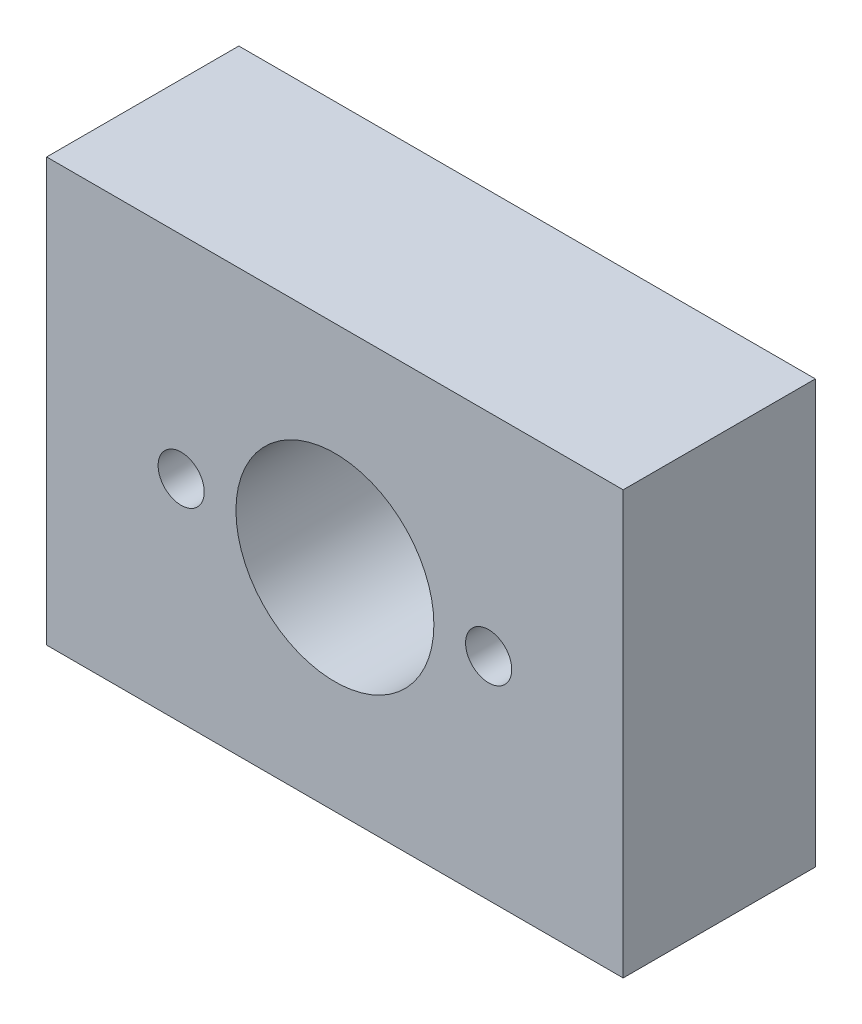
SolidWorks part; units mm, degrees
ref_plane "Front Plane" through (0, 0, 0) normal (0, 0, 1) x (1, 0, 0)
ref_plane "Top Plane" through (0, 0, 0) normal (0, 1, 0) x (1, 0, 0)
ref_plane "Right Plane" through (0, 0, 0) normal (1, 0, 0) x (0, 0, -1)
sketch "Sketch1" plane through (0, 0, 0) normal (0, 0, 1) x (1, 0, 0)
  line L1 (15, -11) -> (-15, -11)
  line L2 (15, -11) -> (15, 11)
  line L3 (15, 11) -> (-15, 11)
  line L4 (-15, -11) -> (-15, 11)
  circle A0 centre (0, 0) radius 11 construction
  circle A1 centre (0, 0) radius 5.15
  point P0 (0, 0)
  point P9 (-15, 0)
  point P10 (0, 11)
  dimension "D1" = 22
  dimension "D4" = 10.3
  dimension "D2" = 11
  dimension "D3" = 30
extrude "Boss-Extrude1" add sketch "Sketch1" along normal blind 10
sketch "Sketch2" plane through (0, -11, 0) normal (0, -1, 0) x (1, 0, 0)
  line L0 (0, 10) -> (0, 0) construction
  line L1 (-15, 10) -> (15, 10) construction
  circle A0 centre (-11, 5) radius 2
  circle A1 centre (11, 5) radius 2
  point P10 (0, 5)
  dimension "D2" = 4
  dimension "D1" = 22
extrude "Cut-Extrude1" cut sketch "Sketch2" against normal blind 10
sketch "Sketch7" plane through (0, 0, 10) normal (0, 0, 1) x (1, 0, 0)
  line L0 (0, 11) -> (0, 0) construction
  line L1 (15, 11) -> (-15, 11) construction
  circle A0 centre (-8, 0) radius 1.2
  circle A1 centre (8, 0) radius 1.2
  dimension "D1" = 2.4
  dimension "D2" = 16
extrude "Cut-Extrude2" cut sketch "Sketch7" against normal through all
